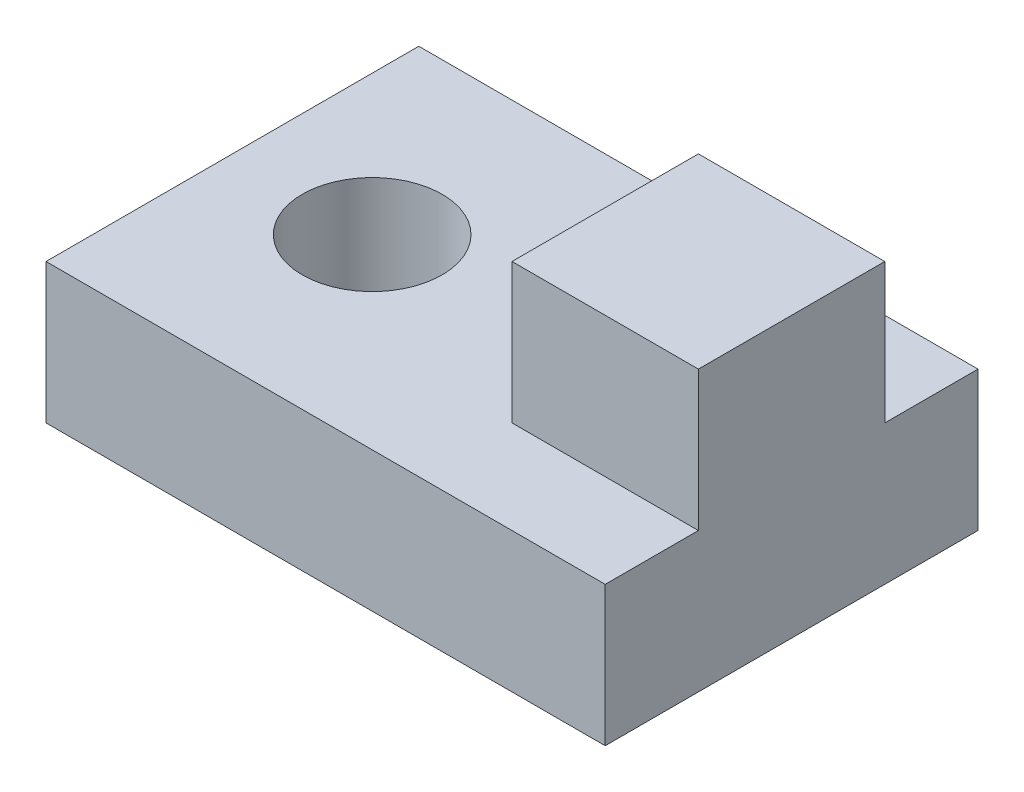
SolidWorks part; units mm, degrees
ref_plane "Front Plane" through (0, 0, 0) normal (0, 0, 1) x (1, 0, 0)
ref_plane "Top Plane" through (0, 0, 0) normal (0, 1, 0) x (1, 0, 0)
ref_plane "Right Plane" through (0, 0, 0) normal (1, 0, 0) x (0, 0, -1)
sketch "Sketch1" plane through (0, 0, 0) normal (0, 1, 0) x (1, 0, 0)
  line L0 (0, 20) -> (0, -20) construction
  line L1 (-30, 20) -> (30, 20)
  line L2 (-30, 20) -> (-30, -20)
  line L3 (-30, -20) -> (30, -20)
  line L4 (30, 20) -> (30, -20)
  line L5 (-30, 0) -> (30, 0) construction
  point P8 (0, 0)
  dimension "D1" = 60
  dimension "D2" = 40
extrude "Boss-Extrude1" add sketch "Sketch1" along normal blind 15
sketch "Sketch2" plane through (0, 15, 0) normal (0, 1, 0) x (1, 0, 0)
  line L0 (-30, 20) -> (-30, -20) construction
  line L1 (-30, -20) -> (30, -20) construction
  circle A0 centre (-15, 0) radius 7.5
  dimension "D2" = 15
  dimension "D1" = 15
  dimension "D3" = 20
extrude "Cut-Extrude1" cut sketch "Sketch2" against normal up to next
sketch "Sketch3" plane through (0, 15, 0) normal (0, 1, 0) x (1, 0, 0)
  line L0 (30, -20) -> (30, 20) construction
  line L1 (30, 10) -> (10, 10)
  line L2 (30, 10) -> (30, -10)
  line L3 (30, -10) -> (10, -10)
  line L4 (10, 10) -> (10, -10)
  line L5 (30, 20) -> (-30, 20) construction
  dimension "D1" = 20
  dimension "D2" = 20
  dimension "D3" = 10
extrude "Boss-Extrude2" add sketch "Sketch3" along normal blind 15
